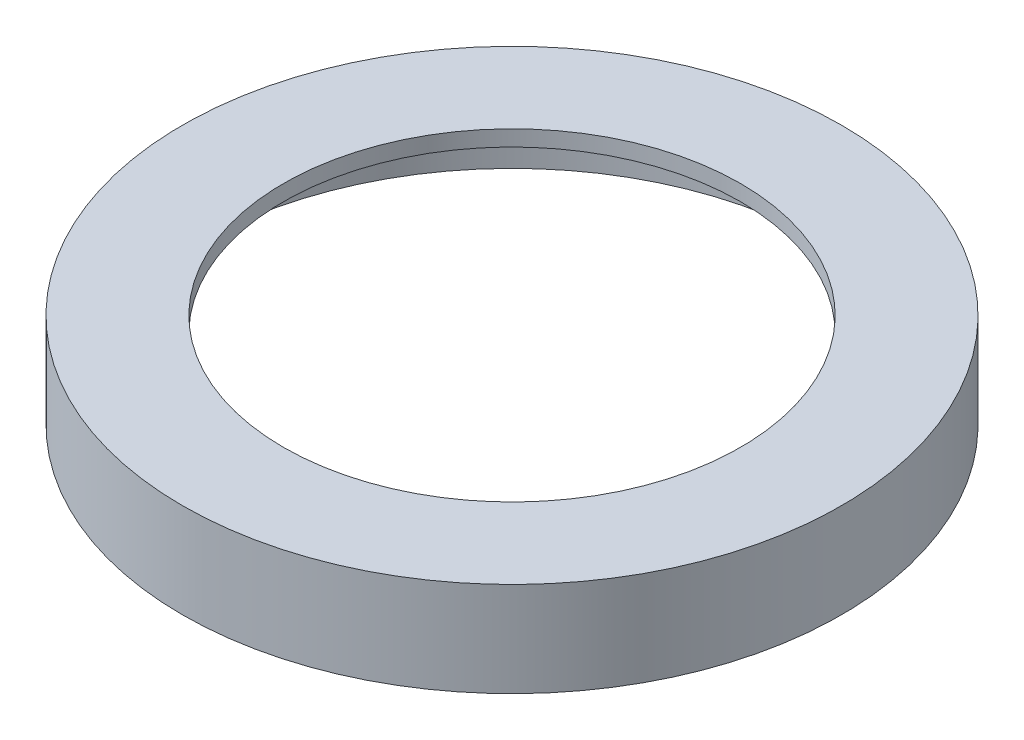
SolidWorks part; units mm, degrees
material "1060 Alloy"
ref_plane "Front Plane" through (0, 0, 0) normal (0, 0, 1) x (1, 0, 0)
ref_plane "Top Plane" through (0, 0, 0) normal (0, 1, 0) x (1, 0, 0)
ref_plane "Right Plane" through (0, 0, 0) normal (1, 0, 0) x (0, 0, -1)
sketch "Sketch1" plane through (0, 0, 0) normal (0, 1, 0) x (1, 0, 0)
  circle A0 centre (0, 0) radius 50.5714
  circle A1 centre (0, 0) radius 53.1114
  dimension "D1" = 101.1428
  dimension "D2" = 2.54
extrude "Boss-Extrude1" add sketch "Sketch1" along normal blind 12.7
sketch "Sketch2" plane through (0, 12.7, 0) normal (0, 1, 0) x (1, 0, 0)
  circle A0 centre (0, 0) radius 53.1114
  circle A1 centre (0, 0) radius 53.1114 construction
  circle A2 centre (0, 0) radius 36.83
  dimension "D1" = 73.66
extrude "Boss-Extrude2" add sketch "Sketch2" along normal blind 2.54
